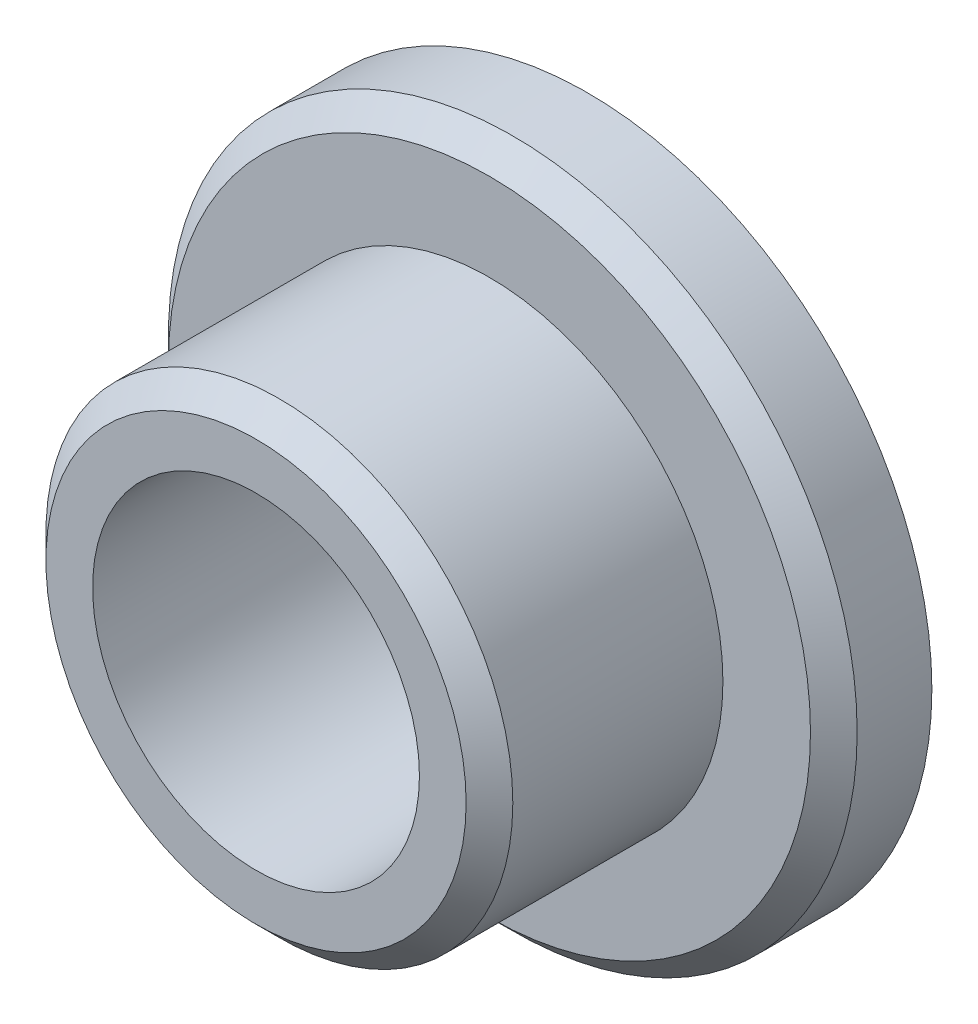
SolidWorks part; units mm, degrees
ref_plane "前视基准面" through (0, 0, 0) normal (0, 0, 1) x (1, 0, 0)
ref_plane "上视基准面" through (0, 0, 0) normal (0, 1, 0) x (1, 0, 0)
ref_plane "右视基准面" through (0, 0, 0) normal (1, 0, 0) x (0, 0, -1)
sketch "草图1" plane through (0, 0, 0) normal (0, 0, 1) x (1, 0, 0)
  circle A0 centre (0, 0) radius 14.75
  dimension "D1" = 29.5
extrude "凸台-拉伸1" add sketch "草图1" along normal blind 4.2
sketch "草图2" plane through (0, 0, 4.2) normal (0, 0, 1) x (1, 0, 0)
  circle A0 centre (0, 0) radius 10
  dimension "D1" = 20
extrude "凸台-拉伸2" add sketch "草图2" along normal blind 10
sketch "草图3" plane through (0, 0, 14.2) normal (0, 0, 1) x (1, 0, 0)
  circle A0 centre (0, 0) radius 7
  dimension "D1" = 14
extrude "切除-拉伸1" cut sketch "草图3" against normal through all
chamfer "倒角1" distance 1 angle 45 2 edges at (10, 0, 14.2) (14.75, 0, 4.2)
